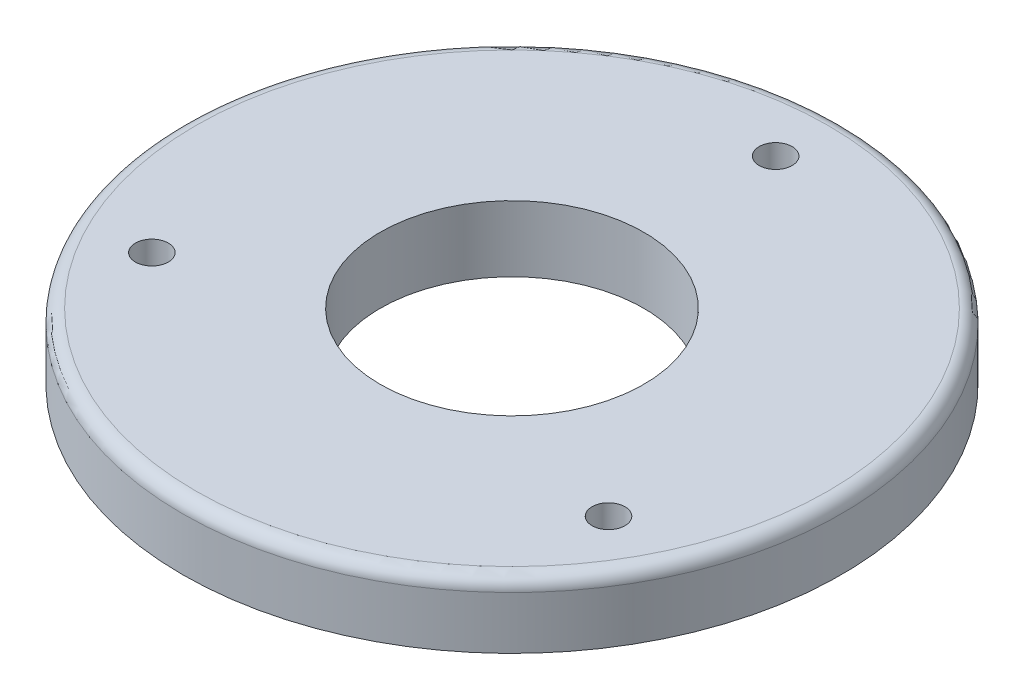
SolidWorks part; units mm, degrees
material "Polyetheretherketone (PEEK)"
ref_plane "Front Plane" through (0, 0, 0) normal (0, 0, 1) x (1, 0, 0)
ref_plane "Top Plane" through (0, 0, 0) normal (0, 1, 0) x (1, 0, 0)
ref_plane "Right Plane" through (0, 0, 0) normal (1, 0, 0) x (0, 0, -1)
sketch "Sketch1" plane through (0, 0, 0) normal (0, 1, 0) x (1, 0, 0)
  circle A0 centre (0, 0) radius 63.5
  dimension "RotatingDiskLid" = 127
extrude "Boss-Extrude1" add sketch "Sketch1" along normal blind 12.7
sketch "Sketch2" plane through (0, 12.7, 0) normal (0, 1, 0) x (1, 0, 0)
  circle A0 centre (0, 0) radius 25.4
  dimension "RotatingDiskLidPegHole" = 50.8
extrude "Cut-Extrude1" cut sketch "Sketch2" against normal through all
sketch "Sketch3" plane through (0, 12.7, 0) normal (0, 1, 0) x (1, 0, 0)
  circle A0 centre (0, 0) radius 50.8 construction
  circle A1 centre (0, 50.8) radius 3.175
  circle A2 centre (43.9941, -25.4) radius 3.175
  circle A3 centre (-43.9941, -25.4) radius 3.175
  point P12 (0, 0)
  dimension "LidBoltHoleCircle" = 101.6
  dimension "D1" = 6.35
  dimension "D2" = 3
extrude "Cut-Extrude2" cut sketch "Sketch3" against normal through all
fillet "Fillet1" radius 2.54 1 edges at (0, 12.7, 63.5)
equation "\"ScopeLengthUnit\"= 10 * \"ScaleFactor\""
equation "\"EyepieceRadius\"= 0.75 * \"ScaleFactor\""
equation "\"ScopeThickness\"= 0.1 * \"ScaleFactor\""
equation "\"ScopeLensWidth\"= 2 * \"ScaleFactor\""
equation "\"ScopeOutsideRadius\"= 2.1 * \"ScaleFactor\""
equation "\"PegWidth\"=1"
equation "\"SupportOutsideDiam\"= \"ScopeOutsideRadius\" * 2 + .25"
equation "\"RotatingDiskDiam\"=3"
equation "\"LegSeatWidth\"=4 "
equation "\"BoltCircleDiam\"= ( \"RotatingDiskDiam\" + \"RotatingDiskHousingDiameter\" ) / 2"
equation "\"RotatingDiskHousingDiameter\"= (\"RotatingDiskDiam\" + 2)"
equation "\"RotatingDiskLid@Sketch1\"=\"RotatingDiskHousingDiameter\""
equation "\"RotatingDiskLidPegHole@Sketch2\"=\"PegWidth\"*2"
equation "\"LidBoltHoleCircle@Sketch3\"=\"BoltCircleDiam\""
equation "\"LegSeatHeight\"=2"
equation "\"LegThickness\"=0.25"
equation "\"LegHeight\"=48"
equation "\"LegBoltDiam\"=0.25"
equation "\"PinHeight\"=\"RotDiskLidHeight\" + \"RotDiskHeight\" + \"PinBoltDiam\"*3"
equation "\"PinBoltDiam\"=0.25"
equation "\"RotDiskHeight\"=0.5"
equation "\"RotDiskLidHeight\"= 0.5"
equation "\"D1@Boss-Extrude1\"=\"RotDiskLidHeight\""
equation "\"DiskSeatPinDiam\"=0.25"
equation "\"D1@Sketch3\"=\"DiskSeatPinDiam\""
equation "\"ScaleFactor\"= 1"
